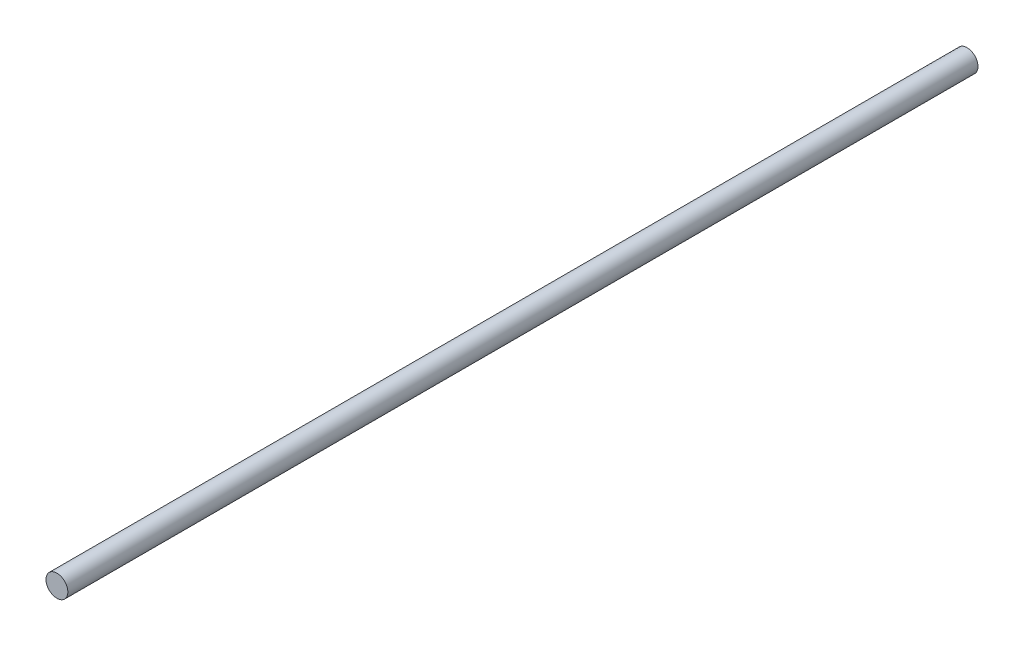
SolidWorks part; units mm, degrees
ref_plane "Alzado" through (0, 0, 0) normal (0, 0, 1) x (1, 0, 0)
ref_plane "Planta" through (0, 0, 0) normal (0, 1, 0) x (1, 0, 0)
ref_plane "Vista lateral" through (0, 0, 0) normal (1, 0, 0) x (0, 0, -1)
sketch "Croquis1" plane through (0, 0, 0) normal (0, 0, 1) x (1, 0, 0)
  circle A0 centre (0, 0) radius 3
  dimension "D1" = 6
extrude "Saliente-Extruir1" add sketch "Croquis1" along normal blind 250
